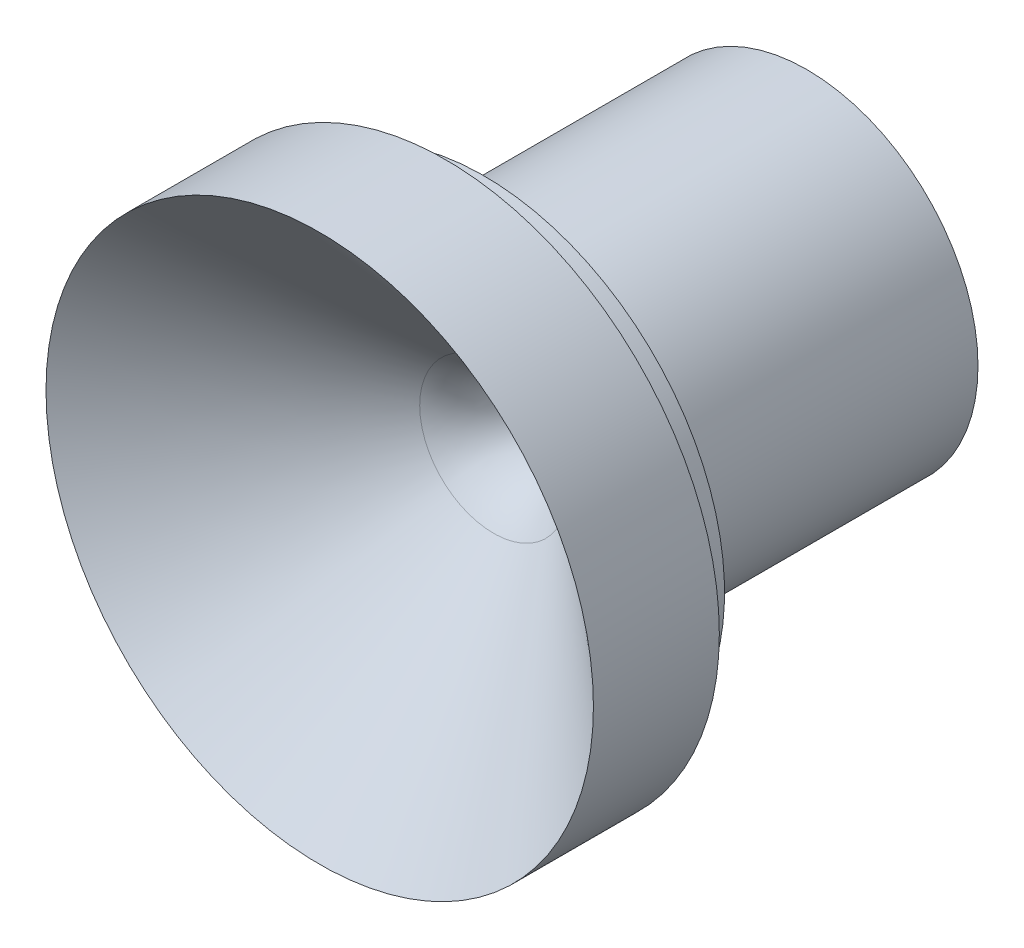
SolidWorks part; units mm, degrees
material "Glass"
ref_plane "Front Plane" through (0, 0, 0) normal (0, 0, 1) x (1, 0, 0)
ref_plane "Top Plane" through (0, 0, 0) normal (0, 1, 0) x (1, 0, 0)
ref_plane "Right Plane" through (0, 0, 0) normal (1, 0, 0) x (0, 0, -1)
sketch "Sketch2" plane through (0, 0, 0) normal (1, 0, 0) x (0, 0, -1)
  line L0 (0, 0) -> (-4809.4236, 0) construction
  line L1 (10.9463, 7.9375) -> (-2.2109, 7.9375)
  line L2 (0, 1.7907) -> (2.794, 1.7907)
  line L3 (2.794, 1.7907) -> (10.9463, 3.9751)
  line L4 (10.9463, 3.9751) -> (10.9463, 7.9375)
  line L5 (-2.2109, 7.9375) -> (-4.0397, 8.6231)
  line L6 (-4.0397, 8.6231) -> (-4.0397, 11.1633)
  line L7 (-4.0397, 11.1633) -> (-5.8177, 11.1633)
  line L8 (-5.8177, 11.1633) -> (-5.8177, 12.7)
  line L9 (-5.8177, 12.7) -> (-11.6597, 12.7)
  line L10 (-11.6597, 12.7) -> (-3.5932, 3.4274)
  arc A0 (-3.5932, 3.4274) -> (0, 1.7907) centre (0, 6.5532) ccw
  point P6 (0, 0)
  dimension "D4" = 9.525
  dimension "D1" = 3.5814
  dimension "D2" = 2.794
  dimension "D3" = 15
  dimension "D5" = 7.9502
  dimension "D6" = 15.875
  dimension "D7" = 25.4
  dimension "D8" = 5.842
  dimension "D9" = 22.606
  dimension "D10" = 7.62
  dimension "D11" = 1.8288
  dimension "D12" = 22.3266
revolve "Revolve1" add sketch "Sketch2" angle 360 about L0
